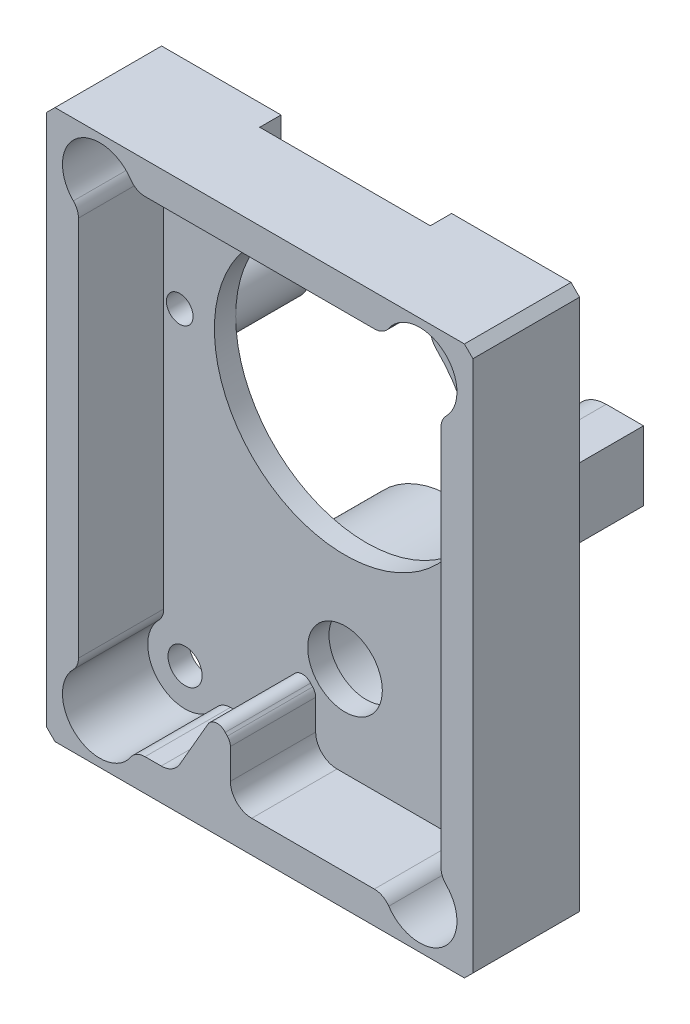
SolidWorks part; units mm, degrees
material "Aluminum"
ref_plane "Front Plane" through (0, 0, 0) normal (0, 0, 1) x (1, 0, 0)
ref_plane "Top Plane" through (0, 0, 0) normal (0, 1, 0) x (1, 0, 0)
ref_plane "Right Plane" through (0, 0, 0) normal (1, 0, 0) x (0, 0, -1)
sketch "Sketch1" plane through (0, 0, 0) normal (0, 0, 1) x (1, 0, 0)
  line L1 (-20, 25.75) -> (20, 25.75)
  line L2 (-20, 25.75) -> (-20, -25.75)
  line L3 (-20, -25.75) -> (20, -25.75)
  line L4 (20, 25.75) -> (20, -25.75)
  line L5 (-20, 25.75) -> (20, -25.75) construction
  line L6 (-20, -25.75) -> (20, 25.75) construction
  point P0 (0, 0)
  dimension "D1" = 51.5
  dimension "D2" = 40
extrude "Boss-Extrude1" add sketch "Sketch1" along normal blind 18
sketch "Sketch3" plane through (0, 0, 18) normal (0, 0, 1) x (1, 0, 0)
  line L0 (20, 25.75) -> (-20, 25.75) construction
  line L1 (-20, -25.75) -> (20, -25.75) construction
  line L2 (-20, 25.75) -> (-20, -25.75) construction
  line L3 (20, -25.75) -> (20, 25.75) construction
  circle A0 centre (-15, 21.5) radius 1.6
  circle A1 centre (-15, -21.5) radius 1.6
  circle A2 centre (15, 21.5) radius 1.6
  circle A3 centre (15, -21.5) radius 1.6
  dimension "D1" = 3.2
  dimension "D2" = 4.25
  dimension "D3" = 4.25
  dimension "D4" = 5
  dimension "D5" = 5
extrude "Cut-Extrude1" cut sketch "Sketch3" against normal through all
sketch "Sketch4" plane through (0, 0, 18) normal (0, 0, 1) x (1, 0, 0)
  line L0 (-20, -25.75) -> (20, -25.75) construction
  circle A0 centre (0, -14.25) radius 3.5
  dimension "D1" = 7
  dimension "D2" = 11.5
extrude "Cut-Extrude2" cut sketch "Sketch4" against normal blind 18
sketch "Sketch5" plane through (0, 0, 18) normal (0, 0, 1) x (1, 0, 0)
  line L0 (-17, 17.8728) -> (-17, -17.8728)
  line L2 (17, -17.8728) -> (17, 17.8728)
  line L4 (-2.75, -17.9241) -> (-2.75, -20.75)
  line L5 (-4.8564, -17.1615) -> (-7.5055, -21.75)
  line L6 (-0.75, -22.75) -> (10.7518, -22.75)
  line L7 (20, -25.75) -> (20, 25.75)
  line L8 (20, 25.75) -> (-20, 25.75)
  line L9 (-20, 25.75) -> (-20, -25.75)
  line L10 (-20, -25.75) -> (20, -25.75)
  line L11 (20, -25.75) -> (20, 25.75) construction
  line L12 (20, 25.75) -> (-20, 25.75) construction
  line L13 (-20, 25.75) -> (-20, -25.75) construction
  line L14 (-20, -25.75) -> (20, -25.75) construction
  line L15 (10.7518, 22.75) -> (-10.7518, 22.75)
  line L16 (17, 22.75) -> (-17, 22.75) construction
  line L17 (-17, 22.75) -> (-17, -22.75) construction
  line L18 (17, -22.75) -> (17, 22.75) construction
  line L19 (-10.7518, -22.75) -> (-9.2376, -22.75)
  line L20 (-17, -22.75) -> (17, -22.75) construction
  circle A0 centre (-15, -21.5) radius 1.6 construction
  circle A1 centre (15, -21.5) radius 1.6 construction
  circle A2 centre (15, 21.5) radius 1.6 construction
  circle A3 centre (-15, 21.5) radius 1.6 construction
  arc A4 (-17.4777, -19.0279) -> (-12.1047, -23.4665) centre (-15, -21.5) ccw
  arc A5 (12.1047, -23.4665) -> (17.4777, -19.0279) centre (15, -21.5) ccw
  arc A6 (17.4777, 19.0279) -> (12.1047, 23.4665) centre (15, 21.5) ccw
  arc A7 (-12.1047, 23.4665) -> (-17.4777, 19.0279) centre (-15, 21.5) ccw
  circle A8 centre (-15, 21.5) radius 3.5 construction
  circle A9 centre (15, 21.5) radius 3.5 construction
  circle A10 centre (15, -21.5) radius 3.5 construction
  circle A11 centre (-15, -21.5) radius 3.5 construction
  arc A12 (-17.4777, -19.0279) -> (-17, -17.8728) centre (-18.6354, -17.8728) ccw
  arc A13 (-10.7518, -22.75) -> (-12.1047, -23.4665) centre (-10.7518, -24.3854) ccw
  arc A14 (10.7518, -22.75) -> (12.1047, -23.4665) centre (10.7518, -24.3854) cw
  arc A15 (17.4777, -19.0279) -> (17, -17.8728) centre (18.6354, -17.8728) cw
  arc A16 (17.4777, 19.0279) -> (17, 17.8728) centre (18.6354, 17.8728) ccw
  arc A17 (12.1047, 23.4665) -> (10.7518, 22.75) centre (10.7518, 24.3854) cw
  arc A18 (-12.1047, 23.4665) -> (-10.7518, 22.75) centre (-10.7518, 24.3854) ccw
  arc A19 (-17.4777, 19.0279) -> (-17, 17.8728) centre (-18.6354, 17.8728) cw
  circle A20 centre (-15, -21.5) radius 1.6 construction
  circle A21 centre (15, -21.5) radius 1.6 construction
  circle A22 centre (15, 21.5) radius 1.6 construction
  circle A23 centre (-15, 21.5) radius 1.6 construction
  arc A24 (-3.2301, -17.0119) -> (-4.8564, -17.1615) centre (-3.9904, -17.6615) ccw
  arc A25 (-2.75, -17.9241) -> (-3.036, -17.224) centre (-3.75, -17.9241) ccw
  arc A26 (-3.036, -17.224) -> (-3.2301, -17.0119) centre (-0.0369, -14.2836) cw
  arc A27 (-7.5055, -21.75) -> (-9.2376, -22.75) centre (-9.2376, -20.75) cw
  arc A28 (-2.75, -20.75) -> (-0.75, -22.75) centre (-0.75, -20.75) ccw
  point P65 (-2.75, -22.75)
  dimension "D1" = 7
  dimension "D6" = 1.6354
  dimension "D11" = 4.2
  dimension "D12" = 2
  dimension "D4" = 3
  dimension "D5" = 3
  dimension "D7" = 16.0096
  dimension "D8" = 8.0885
  dimension "D9" = 16.25
  dimension "D10" = 7.8259
  dimension "D13" = 10.7624
  dimension "D14" = 19.25
  dimension "D3" = 3
extrude "Cut-Extrude3" cut sketch "Sketch5" against normal blind 8
sketch "Sketch6" plane through (0, 0, 0) normal (0, 0, -1) x (-1, 0, 0)
  line L0 (-20, 10.5) -> (-15.5, 10.5)
  line L1 (-15.5, 4) -> (-20, 4)
  line L2 (20, 10.5) -> (15.5, 10.5)
  line L3 (15.5, 4) -> (20, 4)
  line L4 (-20, 25.75) -> (-20, -25.75)
  line L5 (-20, -25.75) -> (20, -25.75)
  line L6 (20, -25.75) -> (20, 25.75)
  line L7 (20, 25.75) -> (-20, 25.75)
  line L8 (-20, 25.75) -> (-20, 10.5)
  line L9 (-20, -25.75) -> (20, -25.75)
  line L10 (20, -25.75) -> (20, 4)
  line L11 (20, 25.75) -> (-20, 25.75)
  line L12 (-20, 4) -> (-20, -25.75)
  line L13 (20, 10.5) -> (20, 25.75)
  line L14 (0, 25.75) -> (0, -25.75) construction
  arc A0 (-15.5, 10.5) -> (-15.5, 4) centre (-15.5, 7.25) cw
  arc A1 (15.5, 10.5) -> (15.5, 4) centre (15.5, 7.25) ccw
  circle A2 centre (0, -14.25) radius 9
  dimension "D2" = 3.25
  dimension "D5" = 18
  dimension "D3" = 31
  dimension "D4" = 33
  dimension "D1" = 0
extrude "Cut-Extrude4" cut sketch "Sketch6" against normal blind 8
sketch "Sketch7" plane through (0, 0, 0) normal (0, 0, -1) x (-1, 0, 0)
  circle A0 centre (0, -14.25) radius 7
  dimension "D1" = 14
extrude "Cut-Extrude5" cut sketch "Sketch7" against normal blind 2.8
sketch "Sketch8" plane through (0, 0, 0) normal (0, 0, -1) x (-1, 0, 0)
  circle A0 centre (0, -14.25) radius 6
  dimension "D1" = 12
extrude "Cut-Extrude6" cut sketch "Sketch8" against normal blind 3.8
sketch "Sketch9" plane through (0, 0, 0) normal (0, 0, -1) x (-1, 0, 0)
  circle A1 centre (0, -14.25) radius 5
  dimension "D1" = 10
extrude "Cut-Extrude7" cut sketch "Sketch9" against normal blind 8
hole_wizard "M3x0.5 Tapped Hole1" positions "Sketch10" profile "Sketch11" tap size "M3x0.5" standard "ANSI Metric" end condition through all
sketch "Sketch10" plane through (0, 0, 0) normal (0, 0, -1) x (-1, 0, 0)
  point P0 (-15.5, 7.25)
  point P3 (15.5, 7.25)
sketch "Sketch11" plane through (15.5, 7.25, 0) normal (1, 0, 0) x (0, 1, 0)
  line L0 (0, 0) -> (0, 18)
  line L1 (0, 18) -> (1.25, 18)
  line L2 (1.25, 18) -> (1.25, 0)
  line L5 (1.25, 0) -> (0, 0)
  line L11 (0, -6.35) -> (0, 107.95) construction
  dimension "Thru Tap Drill Dia." = 2.5
  dimension "Thru Tap Drill Depth" = 18
cosmetic thread "Hole Thread1" parameters "D2"=3
cosmetic thread "Hole Thread2" parameters "D2"=3
sketch "Sketch12" plane through (0, 0, 8) normal (0, 0, -1) x (-1, 0, 0)
  line L0 (0, -25.75) -> (0, 25.75) construction
  line L1 (-20, -25.75) -> (20, -25.75) construction
  line L2 (20, 25.75) -> (-20, 25.75) construction
  line L3 (-8, 17.402) -> (-8, 25.75)
  line L4 (-8, 25.75) -> (8, 25.75)
  line L5 (8, 25.75) -> (8, 17.402)
  arc A0 (-8.5965, 15.9771) -> (8.5965, 15.9771) centre (0, 7.25) ccw
  arc A1 (-15.5, 4) -> (-15.5, 10.5) centre (-15.5, 7.25) ccw construction
  arc A2 (15.5, 10.5) -> (15.5, 4) centre (15.5, 7.25) ccw construction
  arc A4 (8, 17.402) -> (8.5965, 15.9771) centre (10, 17.402) ccw
  arc A5 (-8, 17.402) -> (-8.5965, 15.9771) centre (-10, 17.402) cw
  point P8 (15.5, 7.25)
  point P10 (-15.5, 7.25)
  dimension "D1" = 16
  dimension "D2" = 2
extrude "Cut-Extrude8" cut sketch "Sketch12" against normal up to surface (2 mm away) up to face at (16.75, 7.25, 10)
sketch "Sketch13" plane through (0, 0, 0) normal (0, 0, -1) x (-1, 0, 0)
  line L3 (-20, 10.5) -> (-20, 4)
  line L4 (-20, 4) -> (-15.5, 4)
  line L5 (-15.5, 10.5) -> (-20, 10.5)
  line L6 (-20, 10.5) -> (-20, 4)
  line L7 (-20, 4) -> (-15.5, 4)
  line L8 (-15.5, 10.5) -> (-20, 10.5)
  line L9 (20, 4) -> (20, 10.5)
  line L10 (20, 10.5) -> (15.5, 10.5)
  line L11 (15.5, 4) -> (20, 4)
  line L12 (20, 4) -> (20, 10.5)
  line L13 (20, 10.5) -> (15.5, 10.5)
  line L14 (15.5, 4) -> (20, 4)
  arc A1 (-15.5, 4) -> (-15.5, 10.5) centre (-15.5, 7.25) ccw
  arc A2 (-15.5, 4) -> (-15.5, 10.5) centre (-15.5, 7.25) ccw
  arc A3 (15.5, 10.5) -> (15.5, 4) centre (15.5, 7.25) ccw
  arc A4 (15.5, 10.5) -> (15.5, 4) centre (15.5, 7.25) ccw
  dimension "D1" = 0
  dimension "D2" = 0
extrude "Cut-Extrude9" cut sketch "Sketch13" against normal blind 1
chamfer "Chamfer1" distance 0.8 angle 45 4 edges at (-20, -25.75, 13) (20, -25.75, 13) (-20, 25.75, 13) (20, 25.75, 13)
sketch "Sketch14" plane through (0, 0, 1) normal (0, 0, -1) x (-1, 0, 0)
  line L0 (-20, 4) -> (-15.5, 4) construction
  line L1 (-20, 10.5) -> (-19, 10.5)
  line L2 (-20, 10.5) -> (-20, 4)
  line L3 (-20, 4) -> (-19, 4)
  line L4 (-19, 10.5) -> (-19, 4)
  line L5 (15.5, 4) -> (20, 4) construction
  line L6 (20, 10.5) -> (19, 10.5)
  line L7 (20, 10.5) -> (20, 4)
  line L8 (20, 4) -> (19, 4)
  line L9 (19, 10.5) -> (19, 4)
  dimension "D1" = 1
extrude "Cut-Extrude10" cut sketch "Sketch14" against normal up to surface (7 mm away) up to face at (-9, -14.25, 8)
equation "\"D5@Sketch3\"=\"D4@Sketch3\""
equation "\"D2@Sketch3\"=\"D3@Sketch3\""
equation "\"D4@Sketch5\"=\"D3@Sketch5\""
equation "\"D5@Sketch5\"=\"D3@Sketch5\""
